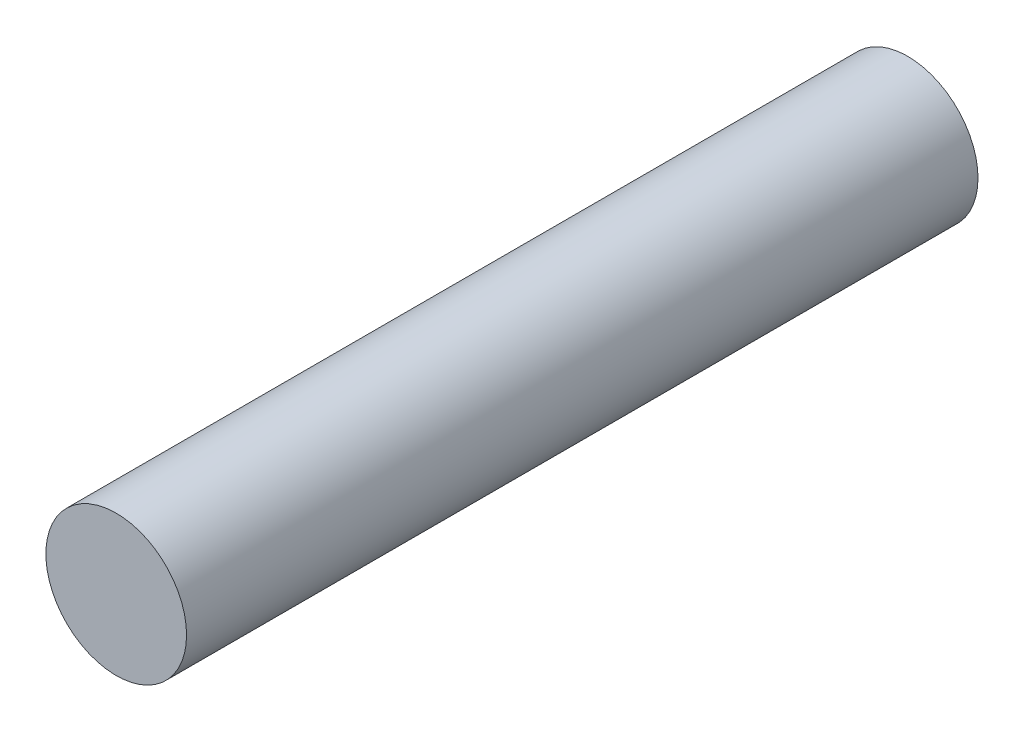
SolidWorks part; units mm, degrees
ref_plane "Front Plane" through (0, 0, 0) normal (0, 0, 1) x (1, 0, 0)
ref_plane "Top Plane" through (0, 0, 0) normal (0, 1, 0) x (1, 0, 0)
ref_plane "Right Plane" through (0, 0, 0) normal (1, 0, 0) x (0, 0, -1)
sketch "Sketch1" plane through (0, 0, 0) normal (0, 0, 1) x (1, 0, 0)
  circle A0 centre (0, 0) radius 4
  dimension "D1" = 8
extrude "Boss-Extrude1" add sketch "Sketch1" along normal blind 45
